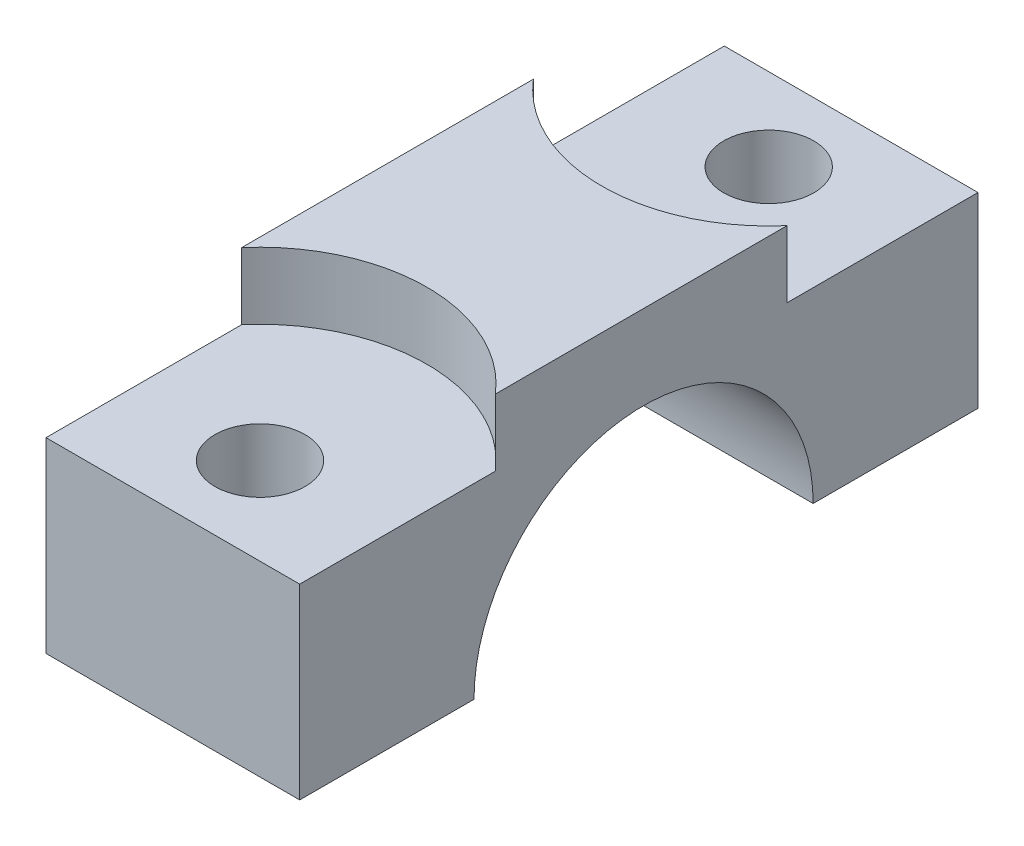
SolidWorks part; units mm, degrees
ref_plane "Plan de face" through (0, 0, 0) normal (0, 0, 1) x (1, 0, 0)
ref_plane "Plan de dessus" through (0, 0, 0) normal (0, 1, 0) x (1, 0, 0)
ref_plane "Plan de droite" through (0, 0, 0) normal (1, 0, 0) x (0, 0, -1)
sketch "Esquisse1" plane through (0, 0, 0) normal (1, 0, 0) x (0, 0, -1)
  line L1 (-25.7544, 19) -> (25.0456, 19)
  line L2 (-25.7544, 19) -> (-25.7544, 0)
  line L3 (-25.7544, 0) -> (25.0456, 0)
  line L4 (25.0456, 19) -> (25.0456, 0)
  circle A0 centre (0, 0) radius 12.7
  dimension "D3" = 25.4
  dimension "D1" = 50.8
  dimension "D2" = 19
extrude "Boss.-Extru.1" add sketch "Esquisse1" along normal mid plane 19 contours A0 L3 L4 L1 L2
sketch "Esquisse3" plane through (0, 0, 0) normal (0, -1, 0) x (1, 0, 0)
  line L0 (0, 12.7) -> (0, 25.7544) construction
  line L1 (9.5, 12.7) -> (-9.5, 12.7) construction
  line L2 (9.5, 25.7544) -> (-9.5, 25.7544) construction
  line L3 (0, -12.7) -> (0, -25.0456) construction
  line L4 (9.5, -12.7) -> (-9.5, -12.7) construction
  line L5 (9.5, -25.0456) -> (-9.5, -25.0456) construction
  point P12 (0, 19.2272)
  point P13 (0, -18.8728)
  point P14 (0, 0)
sketch "Esquisse6" plane through (0, 19, 0) normal (0, 1, 0) x (1, 0, 0)
  line L0 (0, -12.7) -> (0, -25.7544) construction
  line L1 (0, 12.7) -> (0, 25.0456) construction
  point P0 (0, -19.2272)
  point P1 (0, 18.8728)
hole_wizard "Chambrage pour vis à tête hexagonale M123" positions "Esquisse3D4" profile "Esquisse8" counterbore size "M12" standard "ISO" end condition through all
sketch3d "Esquisse3D4"
  point P0 (0, 19, 19.2272)
  point P3 (0, 19, -18.8728)
sketch "Esquisse8" plane through (0, 19, 19.2272) normal (1, 0, 0) x (0, 0, 1)
  line L0 (0, 0) -> (0, 19)
  line L1 (0, 19) -> (3.375, 19)
  line L3 (3.375, 19) -> (3.375, 5)
  line L4 (3.375, 5) -> (12.5, 5)
  line L5 (12.5, 5) -> (12.5, 0)
  line L7 (12.5, 0) -> (0, 0)
  line L11 (0, -6.35) -> (0, 107.95) construction
  dimension "Diamètre du perçage jusqu'au prochain" = 6.75
  dimension "Profondeur du perçage jusqu'au prochain" = 19
  dimension "Diamètre du chambrage" = 25
  dimension "Profondeur du chambrage" = 5
